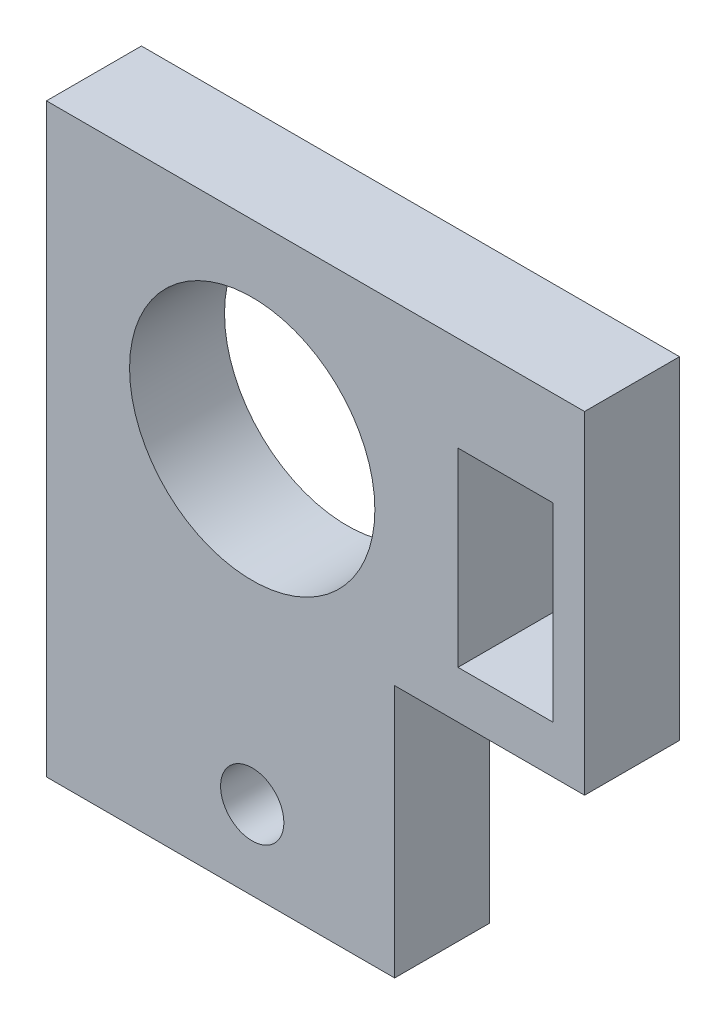
SolidWorks part; units mm, degrees
ref_plane "Front Plane" through (0, 0, 0) normal (0, 0, 1) x (1, 0, 0)
ref_plane "Top Plane" through (0, 0, 0) normal (0, 1, 0) x (1, 0, 0)
ref_plane "Right Plane" through (0, 0, 0) normal (1, 0, 0) x (0, 0, -1)
sketch "Sketch3" plane through (0, 0, 0) normal (0, 0, 1) x (1, 0, 0)
  line L0 (2.5, -9.25) -> (2.5, -1.25)
  line L1 (-8.5, 9.25) -> (8.5, 9.25)
  line L2 (-8.5, 9.25) -> (-8.5, -9.25)
  line L3 (-8.5, -9.25) -> (2.5, -9.25)
  line L4 (8.5, 9.25) -> (8.5, -1.25)
  line L5 (2.5, -1.25) -> (8.5, -1.25)
  point P0 (0, 0)
  dimension "D1" = 17
  dimension "D2" = 18.5
  dimension "D3" = 6
  dimension "D4" = 10.5
extrude "Boss-Extrude3" add sketch "Sketch3" along normal blind 3
sketch "Sketch6" plane through (0, 0, 3) normal (0, 0, 1) x (1, 0, 0)
  line L0 (8.5, -1.25) -> (8.5, 9.25) construction
  line L1 (4.5, 6.25) -> (7.5, 6.25)
  line L2 (4.5, 6.25) -> (4.5, 0.25)
  line L3 (4.5, 0.25) -> (7.5, 0.25)
  line L4 (7.5, 6.25) -> (7.5, 0.25)
  line L5 (2.5, -1.25) -> (8.5, -1.25) construction
  dimension "D1" = 3
  dimension "D2" = 1
  dimension "D3" = 1.5
  dimension "D4" = 6
extrude "Cut-Extrude2" cut sketch "Sketch6" against normal blind 3
sketch "Sketch7" plane through (0, 0, 3) normal (0, 0, 1) x (1, 0, 0)
  line L0 (8.5, 9.25) -> (-8.5, 9.25) construction
  line L1 (-8.5, 9.25) -> (-8.5, -9.25) construction
  line L2 (-8.5, -9.25) -> (2.5, -9.25) construction
  circle A0 centre (-2, 3.25) radius 3.875
  circle A1 centre (-2, -6.75) radius 1
  point P8 (-5.8168, 2.7771)
  point P11 (0, 0)
  point P13 (-8.5, -8.815)
  dimension "D3" = 7.75
  dimension "D6" = 2
  dimension "D1" = 6
  dimension "D2" = 6.5
  dimension "D4" = 2.5
  dimension "D5" = 6.5
extrude "Cut-Extrude3" cut sketch "Sketch7" against normal blind 3
